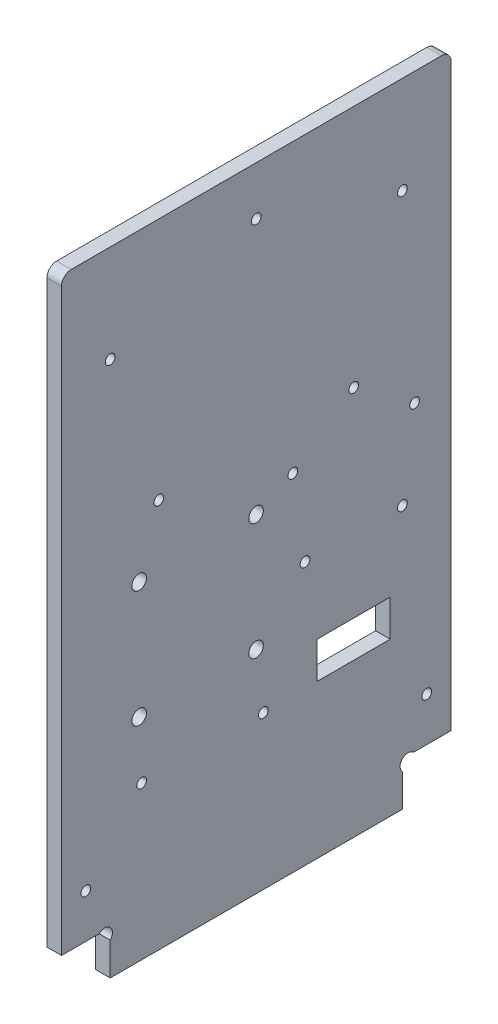
SolidWorks part; units mm, degrees
ref_plane "Plan de face" through (0, 0, 0) normal (0, 0, 1) x (1, 0, 0)
ref_plane "Plan de dessus" through (0, 0, 0) normal (0, 1, 0) x (1, 0, 0)
ref_plane "Plan de droite" through (0, 0, 0) normal (1, 0, 0) x (0, 0, -1)
sketch "Esquisse1" plane through (0, 0, 0) normal (1, 0, 0) x (0, 0, -1)
  line L8 (10, 6.7373) -> (10, 0)
  line L9 (70, 6.7373) -> (70, 0)
  line L10 (7.7373, 9) -> (0, 9)
  line L11 (10, 0) -> (70, 0)
  line L12 (72.2627, 9) -> (80, 9)
  line L13 (0, 9) -> (0, 130)
  line L14 (0, 130) -> (80, 130)
  line L15 (80, 130) -> (80, 9)
  arc A0 (10, 6.7373) -> (7.7373, 9) centre (8.8686, 7.8686) ccw
  arc A1 (70, 6.7373) -> (72.2627, 9) centre (71.1314, 7.8686) cw
  dimension "D7" = 1.1314
  dimension "D6" = 1.6
  dimension "D1" = 9
  dimension "D2" = 10
  dimension "D3" = 10
  dimension "D4" = 80
  dimension "D5" = 130
  dimension "D8" = 1.1314
  dimension "D9" = 1.1314
  dimension "D10" = 1.1314
extrude "Extrusion1" add sketch "Esquisse1" along normal blind 3
sketch "Esquisse2" plane through (3, 0, 0) normal (1, 0, 0) x (0, 0, -1)
  line L0 (0, 9) -> (7.7373, 9) construction
  line L1 (0, 130) -> (0, 9) construction
  line L2 (80, 9) -> (80, 130) construction
  line L3 (72.2627, 9) -> (80, 9) construction
  line L4 (80, 130) -> (0, 130) construction
  circle A0 centre (60, 80) radius 1
  circle A1 centre (10, 110) radius 1
  circle A2 centre (20, 80) radius 1
  circle A3 centre (70, 110) radius 1
  circle A4 centre (15.95, 67.45) radius 1.5
  circle A5 centre (15.95, 43.45) radius 1.5
  circle A6 centre (39.95, 43.45) radius 1.5
  circle A7 centre (39.95, 67.45) radius 1.5
  circle A8 centre (40, 120) radius 1
  circle A9 centre (70, 54) radius 1
  circle A10 centre (50, 54) radius 1
  dimension "D5" = 15.95
  dimension "D7" = 10
  dimension "D9" = 10
  dimension "D4" = 3
  dimension "D6" = 2
  dimension "D1" = 58.45
  dimension "D2" = 24
  dimension "D3" = 24
  dimension "D8" = 40
  dimension "D10" = 30
  dimension "D11" = 10
  dimension "D12" = 20
  dimension "D13" = 10
  dimension "D14" = 10
  dimension "D15" = 10
  dimension "D16" = 20
  dimension "D17" = 45
extrude "Enlèv. mat.-Extru.1" cut sketch "Esquisse2" against normal through all
sketch "Esquisse3" plane through (0, 0, 0) normal (-1, 0, 0) x (0, 0, 1)
  line L1 (-67.5, 39) -> (-52.5, 39)
  line L2 (-67.5, 39) -> (-67.5, 31.5)
  line L3 (-67.5, 31.5) -> (-52.5, 31.5)
  line L4 (-52.5, 39) -> (-52.5, 31.5)
  circle A0 centre (-70, 54) radius 1 construction
  circle A1 centre (-50, 54) radius 1 construction
  dimension "D4" = 2.5
  dimension "D1" = 15
  dimension "D2" = 7.5
  dimension "D3" = 15
  dimension "D5" = 2.5
extrude "Enlèv. mat.-Extru.2" cut sketch "Esquisse3" against normal through all
sketch "Esquisse4" plane through (3, 0, 0) normal (1, 0, 0) x (0, 0, -1)
  line L3 (0, 9) -> (7.7373, 9) construction
  line L4 (0, 130) -> (0, 9) construction
  line L5 (80, 9) -> (80, 130) construction
  circle A2 centre (75, 18) radius 1
  circle A3 centre (5, 18) radius 1
  dimension "D1" = 5
  dimension "D3" = 2
  dimension "D2" = 5
  dimension "D5" = 9
extrude "Enlèv. mat.-Extru.3" cut sketch "Esquisse4" against normal through all
fillet "Congé1" radius 2 2 edges at (1.5, 130, -80) (1.5, 130, 0)
sketch "Esquisse5" plane through (3, 0, 0) normal (1, 0, 0) x (0, 0, -1)
  line L0 (52.5, 31.5) -> (52.5, 39) construction
  line L1 (67.5, 39) -> (67.5, 31.5) construction
  circle A0 centre (16.45, 31.45) radius 1
  circle A1 centre (41.45, 31.45) radius 1
  circle A2 centre (47.5, 71) radius 1
  circle A3 centre (72.5, 71) radius 1
  circle A4 centre (15.95, 43.45) radius 1.5 construction
  circle A7 centre (50, 54) radius 1 construction
  point P12 (0, 0)
  point P15 (0, 0)
  point P16 (0, 0)
  dimension "D1" = 2
  dimension "D2" = 0.5
  dimension "D5" = 12
  dimension "D6" = 5
  dimension "D3" = 25
  dimension "D4" = 17
  dimension "D7" = 5
extrude "Enlèv. mat.-Extru.6" cut sketch "Esquisse5" against normal through all
